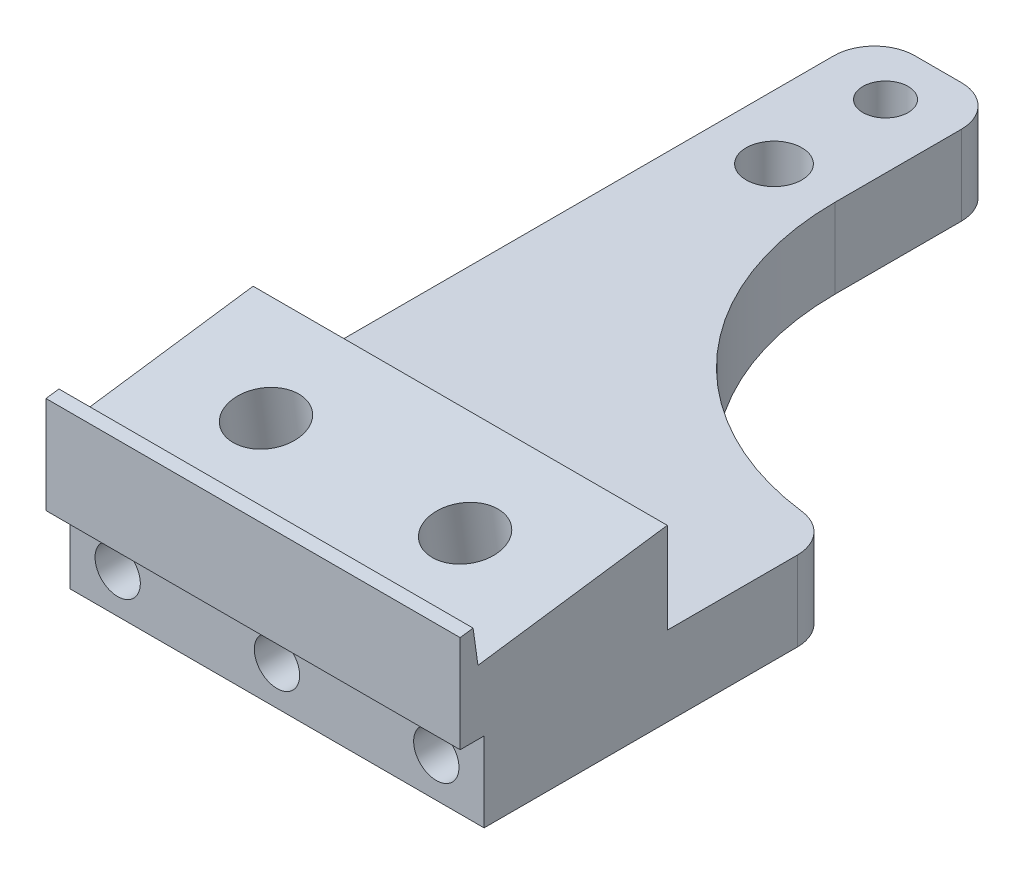
SolidWorks part; units mm, degrees
material "6061-T6 Al"
ref_plane "Front" through (0, 0, 0) normal (0, 0, 1) x (1, 0, 0)
ref_plane "Top" through (0, 0, 0) normal (0, 1, 0) x (1, 0, 0)
ref_plane "Right" through (0, 0, 0) normal (1, 0, 0) x (0, 0, -1)
sketch "Sketch1" plane through (0, 0, 0) normal (0, 1, 0) x (1, 0, 0)
  line L1 (0, 0) -> (-26, 0)
  line L2 (0, 0) -> (0, 51.5)
  line L3 (0, 51.5) -> (-26, 51.5)
  line L4 (-26, 0) -> (-26, 51.5)
  dimension "D1" = 26
  dimension "D2" = 51.5
extrude "Extrude1" add sketch "Sketch1" along normal blind 5
sketch "Sketch2" plane through (0, 5, 0) normal (0, 1, 0) x (1, 0, 0)
  line L1 (0, 51.5) -> (-18, 51.5)
  line L2 (0, 51.5) -> (0, 23.2)
  line L3 (0, 23.2) -> (-18, 23.2)
  line L4 (-18, 51.5) -> (-18, 23.2)
  dimension "D1" = 28.3
  dimension "D2" = 18
extrude "Extrude2" cut sketch "Sketch2" against normal blind 5
fillet "Fillet1" radius 2.54 3 edges at (-26, 2.5, -51.5) (-18, 2.5, -51.5) (0, 2.5, -23.2)
fillet "Fillet2" radius 18 1 edges at (-18, 2.5, -23.2)
sketch "Sketch3" plane through (0, 0, 0) normal (1, 0, 0) x (0, 0, -1)
  line L0 (0, 5) -> (12.5, 5)
  line L1 (0, 5) -> (20.66, 5) construction
  line L2 (12.5, 5) -> (12.5, 10.7)
  line L3 (12.5, 10.7) -> (0.6168, 9.0299)
  line L4 (0.6168, 9.0299) -> (0.3106, 11.2085)
  line L5 (0, 5) -> (0, 11.1649)
  line L6 (0, 11.1649) -> (0.3106, 11.2085)
  dimension "D1" = 8
  dimension "D2" = 5.7
  dimension "D3" = 12.5
  dimension "D4" = 12
  dimension "D5" = 2.2
extrude "Extrude3" add sketch "Sketch3" against normal through all
sketch "Sketch4" plane through (0, 0, 0) normal (0, 0, 1) x (1, 0, 0)
  line L1 (-26, 0) -> (0, 0)
  line L2 (-26, 0) -> (-26, 5)
  line L3 (-26, 5) -> (0, 5)
  line L4 (0, 0) -> (0, 5)
  dimension "D1" = 5
extrude "Extrude4" cut sketch "Sketch4" against normal blind 1
ref_plane "Plane1" through (-13, 0, 0) normal (1, 0, 0) x (0, 0, -1)
hole_wizard "#4-40 Tapped Hole1" positions "3DSketch1" profile "Sketch5" tap size "#4-40" standard "Ansi Inch"
sketch3d "3DSketch1"
  point P0 (-22, 5, -48.2)
  dimension "D1" = 4
  dimension "D2" = 47.2
sketch "Sketch5" plane through (-22, 5, -48.2) normal (1, 0, 0) x (0, 0, 1)
  line L0 (0, 0) -> (0, 10.8138)
  line L1 (0, 10.8138) -> (1.1303, 10.1346)
  line L2 (1.1303, 10.1346) -> (1.1303, 8.2296)
  line L3 (1.1303, 8.2296) -> (1.4224, 8.2296)
  line L4 (1.4224, 8.2296) -> (1.4224, 0)
  line L5 (1.4224, 0) -> (0, 0)
  line L10 (0, 10.8138) -> (-1.1303, 10.1346) construction
  line L11 (0, -6.35) -> (0, 107.95) construction
  dimension "Tap Drill Dia." = 2.2606
  dimension "Tap Drill Depth" = 10.1346
  dimension "Thread Major Dia." = 2.8448
  dimension "Thread Depth" = 8.2296
  dimension "Drill Angle" = 118
sketch "Sketch6" plane through (0, 5, 0) normal (0, 1, 0) x (1, 0, 0)
  line L0 (-26, 48.96) -> (-26, 12.5) construction
  circle A0 centre (-22, 41.2) radius 1.75
  circle A1 centre (-22, 48.2) radius 1.4224 construction
  dimension "D1" = 3.5
  dimension "D2" = 4
  dimension "D3" = 7
extrude "Extrude5" cut sketch "Sketch6" against normal through all
hole_wizard "#8-32 Tapped Hole1" positions "3DSketch2" profile "Sketch7" tap size "#8-32" standard "Ansi Inch"
sketch3d "3DSketch2"
  line L0 (-26, 10.7, -12.5) -> (0, 10.7, -12.5) construction
  point P0 (-19.25, 9.865, -6.5584)
  point P2 (-6.75, 9.865, -6.5584)
  dimension "D1" = 6.25
  dimension "D2" = 6.25
  dimension "D3" = 6
sketch "Sketch7" plane through (-19.25, 9.865, -6.5584) normal (1, 0, 0) x (0, -0.1392, 0.9903)
  line L0 (0, 0) -> (0, 11.7566)
  line L1 (0, 11.7566) -> (1.7272, 10.7188)
  line L2 (1.7272, 10.7188) -> (1.7272, 8.3312)
  line L3 (1.7272, 8.3312) -> (2.0828, 8.3312)
  line L4 (2.0828, 8.3312) -> (2.0828, 0)
  line L5 (2.0828, 0) -> (0, 0)
  line L10 (0, 11.7566) -> (-1.7272, 10.7188) construction
  line L11 (0, -6.35) -> (0, 107.95) construction
  dimension "Tap Drill Dia." = 3.4544
  dimension "Tap Drill Depth" = 10.7188
  dimension "Thread Major Dia." = 4.1656
  dimension "Thread Depth" = 8.3312
  dimension "Drill Angle" = 118
hole_wizard "#4-40 Tapped Hole2" positions "3DSketch3" profile "Sketch8" tap size "#4-40" standard "Ansi Inch"
sketch3d "3DSketch3"
  line L0 (0, 5, -1) -> (-26, 5, -1) construction
  point P0 (-23, 2.5, -1)
  point P2 (-13, 2.5, -1)
  point P4 (-3, 2.5, -1)
  dimension "D1" = 10
  dimension "D2" = 10
  dimension "D3" = 2.5
sketch "Sketch8" plane through (-23, 2.5, -1) normal (1, 0, 0) x (0, -1, 0)
  line L0 (0, 0) -> (0, 9.5692)
  line L1 (0, 9.5692) -> (1.1303, 8.89)
  line L2 (1.1303, 8.89) -> (1.1303, 5.6896)
  line L3 (1.1303, 5.6896) -> (1.4224, 5.6896)
  line L4 (1.4224, 5.6896) -> (1.4224, 0)
  line L5 (1.4224, 0) -> (0, 0)
  line L10 (0, 9.5692) -> (-1.1303, 8.89) construction
  line L11 (0, -6.35) -> (0, 107.95) construction
  dimension "Tap Drill Dia." = 2.2606
  dimension "Tap Drill Depth" = 8.89
  dimension "Thread Major Dia." = 2.8448
  dimension "Thread Depth" = 5.6896
  dimension "Drill Angle" = 118
sketch "Sketch9" plane through (0, 0, 0) normal (0, -1, 0) x (1, 0, 0)
  line L0 (-13, -6.1407) -> (-13, 6.1407) construction
  line L1 (-26, -1) -> (0, -1) construction
  circle A0 centre (-23, -9.89) radius 0.5
  circle A1 centre (-13, -9.89) radius 0.5
  circle A2 centre (-3, -9.89) radius 0.5
  dimension "D1" = 1
  dimension "D2" = 1
  dimension "D3" = 1
  dimension "D4" = 10
  dimension "D5" = 10
  dimension "D6" = 8.89
extrude "Extrude6" cut sketch "Sketch9" against normal blind 2.032
sketch "Sketch12" plane through (0, 0, 0) normal (1, 0, 0) x (0, 0, -1)
  line L0 (0, 11.1649) -> (-0.5, 11.0946)
  line L1 (-0.5, 11.0946) -> (-0.5, 5)
  line L2 (-0.5, 5) -> (0, 5)
  line L3 (0, 5) -> (0, 11.1649)
  line L4 (0.3106, 11.2085) -> (0, 11.1649) construction
  dimension "D1" = 0.5
extrude "Boss-Extrude2" add sketch "Sketch12" against normal up to surface (26 mm away) up to face at (-26, 5.9253, -14.4077)
